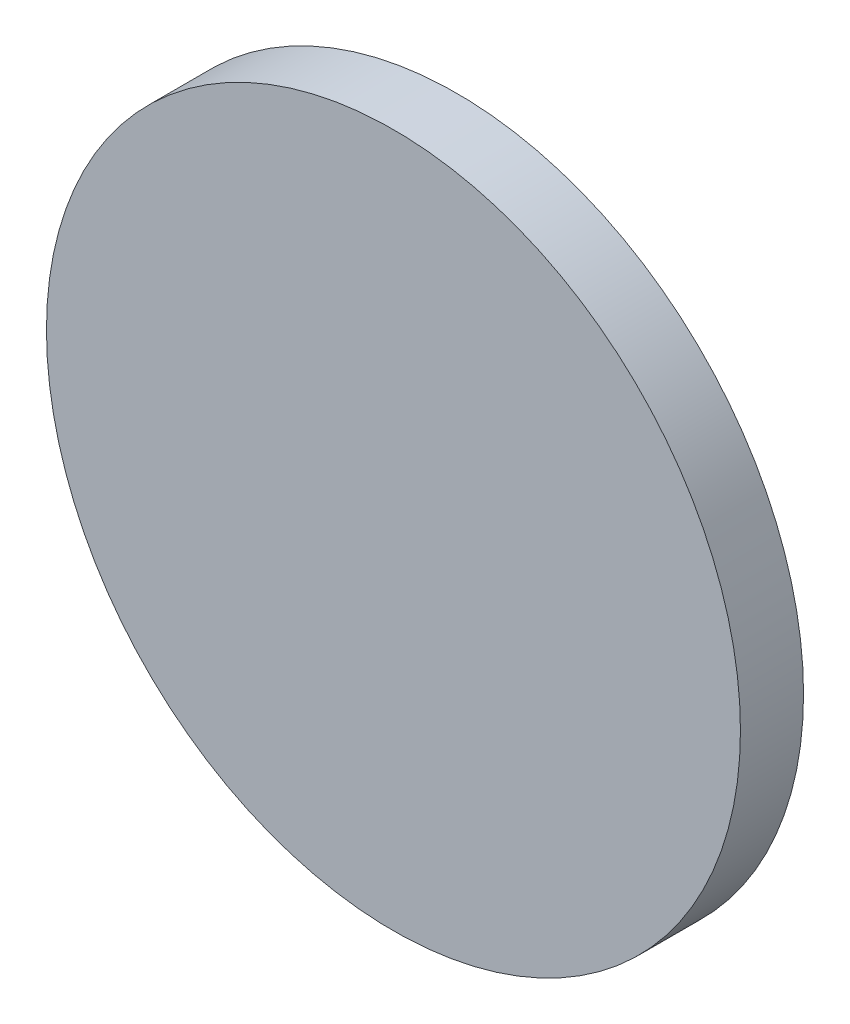
SolidWorks part; units mm, degrees
ref_plane "Front Plane" through (0, 0, 0) normal (0, 0, 1) x (1, 0, 0)
ref_plane "Top Plane" through (0, 0, 0) normal (0, 1, 0) x (1, 0, 0)
ref_plane "Right Plane" through (0, 0, 0) normal (1, 0, 0) x (0, 0, -1)
sketch "Sketch1" plane through (0, 0, 0) normal (0, 0, 1) x (1, 0, 0)
  circle A0 centre (0, -17.75) radius 11
  dimension "D1" = 0
  dimension "D2" = 22
extrude "Boss-Extrude1" add sketch "Sketch1" along normal blind 2
